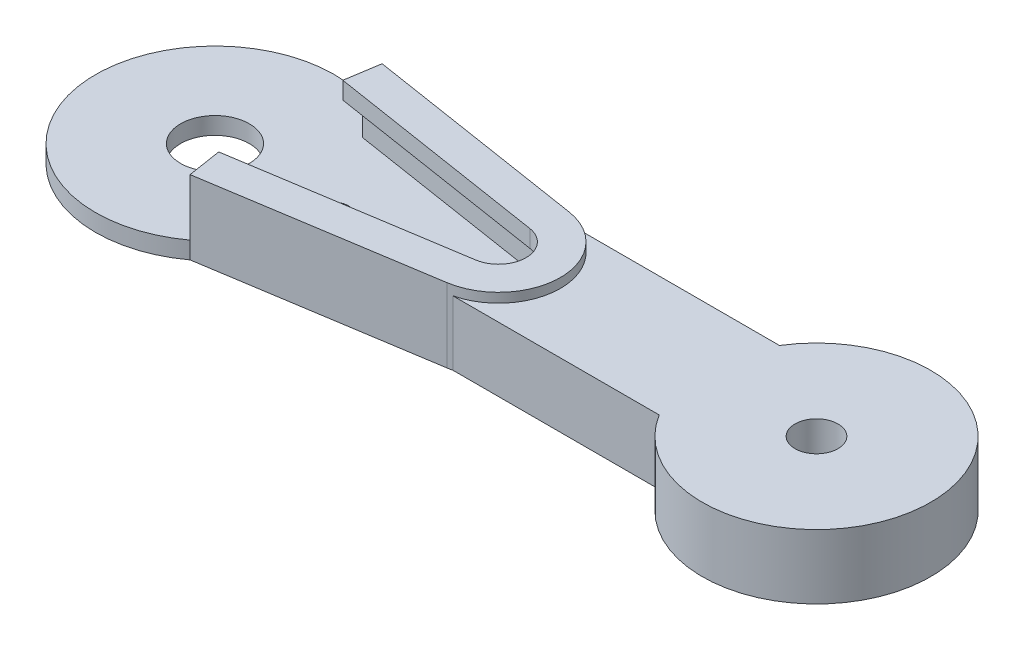
SolidWorks part; units mm, degrees
ref_plane "Front Plane" through (0, 0, 0) normal (0, 0, 1) x (1, 0, 0)
ref_plane "Top Plane" through (0, 0, 0) normal (0, 1, 0) x (1, 0, 0)
ref_plane "Right Plane" through (0, 0, 0) normal (1, 0, 0) x (0, 0, -1)
sketch "Sketch2" plane through (0, 0, 0) normal (0, 1, 0) x (1, 0, 0)
  circle A0 centre (0, 0) radius 6
  circle A1 centre (0, 0) radius 1.5
  dimension "D1" = 12
  dimension "D2" = 3
extrude "Boss-Extrude1" add sketch "Sketch2" along normal mid plane 2.3
sketch "Sketch3" plane through (0, 1.15, 0) normal (0, 1, 0) x (1, 0, 0)
  line L0 (0, 0) -> (0, 2.9) construction
  line L3 (0, 0) -> (0.376, 2.9763) construction
  line L52 (0.1074, 2.898) -> (0.3384, 2.6787)
  line L53 (-0.1074, 2.898) -> (-0.3384, 2.6787)
  line L54 (0.8248, 2.7802) -> (0.9939, 2.5104)
  line L55 (0.6167, 2.8337) -> (0.3384, 2.6787)
  line L56 (1.4903, 2.4878) -> (1.587, 2.1843)
  line L57 (1.302, 2.5913) -> (0.9939, 2.5104)
  line L58 (2.0621, 2.039) -> (2.0804, 1.721)
  line L59 (1.9055, 2.1861) -> (1.587, 2.1843)
  line L60 (2.5044, 1.4621) -> (2.443, 1.1496)
  line L61 (2.3893, 1.6435) -> (2.0804, 1.721)
  line L62 (2.7894, 0.7934) -> (2.6522, 0.5059)
  line L63 (2.723, 0.9977) -> (2.443, 1.1496)
  line L64 (2.899, 0.0748) -> (2.6947, -0.1695)
  line L65 (2.8855, 0.2892) -> (2.6522, 0.5059)
  line L66 (2.8265, -0.6486) -> (2.5679, -0.8343)
  line L67 (2.8668, -0.4375) -> (2.6947, -0.1695)
  line L68 (2.5765, -1.3311) -> (2.2797, -1.4467)
  line L69 (2.6679, -1.1367) -> (2.5679, -0.8343)
  line L70 (2.1645, -1.93) -> (1.8483, -1.9682)
  line L71 (2.3014, -1.7645) -> (2.2797, -1.4467)
  line L72 (1.6165, -2.4077) -> (1.3007, -2.366)
  line L73 (1.7903, -2.2814) -> (1.8483, -1.9682)
  line L74 (0.967, -2.734) -> (0.6715, -2.6152)
  line L75 (1.1667, -2.655) -> (1.3007, -2.366)
  line L76 (0.2566, -2.8886) -> (0, -2.7)
  line L77 (0.4698, -2.8617) -> (0.6715, -2.6152)
  line L78 (-0.4698, -2.8617) -> (-0.6715, -2.6152)
  line L79 (-0.2566, -2.8886) -> (0, -2.7)
  line L80 (-1.1667, -2.655) -> (-1.3007, -2.366)
  line L81 (-0.967, -2.734) -> (-0.6715, -2.6152)
  line L82 (-1.7903, -2.2814) -> (-1.8483, -1.9682)
  line L83 (-1.6165, -2.4077) -> (-1.3007, -2.366)
  line L84 (-2.3014, -1.7645) -> (-2.2797, -1.4467)
  line L85 (-2.1645, -1.93) -> (-1.8483, -1.9682)
  line L86 (-2.6679, -1.1367) -> (-2.5679, -0.8343)
  line L87 (-2.5765, -1.3311) -> (-2.2797, -1.4467)
  line L88 (-2.8668, -0.4375) -> (-2.6947, -0.1695)
  line L89 (-2.8265, -0.6486) -> (-2.5679, -0.8343)
  line L90 (-2.8855, 0.2892) -> (-2.6522, 0.5059)
  line L91 (-2.899, 0.0748) -> (-2.6947, -0.1695)
  line L92 (-2.723, 0.9977) -> (-2.443, 1.1496)
  line L93 (-2.7894, 0.7934) -> (-2.6522, 0.5059)
  line L94 (-2.3893, 1.6435) -> (-2.0804, 1.721)
  line L95 (-2.5044, 1.4621) -> (-2.443, 1.1496)
  line L96 (-1.9055, 2.1861) -> (-1.587, 2.1843)
  line L97 (-2.0621, 2.039) -> (-2.0804, 1.721)
  line L98 (-1.302, 2.5913) -> (-0.9939, 2.5104)
  line L99 (-1.4903, 2.4878) -> (-1.587, 2.1843)
  line L100 (-0.6167, 2.8337) -> (-0.3384, 2.6787)
  line L101 (-0.8248, 2.7802) -> (-0.9939, 2.5104)
  line L102 (-2.533, 1.6075) -> (-2.3893, 1.6435) construction
  line L103 (-2.533, 1.6075) -> (-2.5044, 1.4621) construction
  line L104 (-2.8532, 0.9271) -> (-2.723, 0.9977) construction
  line L105 (-2.8532, 0.9271) -> (-2.7894, 0.7934) construction
  line L106 (-2.9941, 0.1884) -> (-2.8855, 0.2892) construction
  line L107 (-2.9941, 0.1884) -> (-2.899, 0.0748) construction
  line L108 (-2.9469, -0.5621) -> (-2.8668, -0.4375) construction
  line L109 (-2.9469, -0.5621) -> (-2.8265, -0.6486) construction
  line L110 (0, 3) -> (0.1074, 2.898) construction
  line L111 (0, 2.9) -> (0, 3) construction
  line L112 (0, 3) -> (-0.1074, 2.898) construction
  line L113 (-0.7461, 2.9057) -> (-0.6167, 2.8337) construction
  line L114 (-0.7461, 2.9057) -> (-0.8248, 2.7802) construction
  line L115 (-1.4453, 2.6289) -> (-1.302, 2.5913) construction
  line L116 (-1.4453, 2.6289) -> (-1.4903, 2.4878) construction
  line L117 (-2.0536, 2.1869) -> (-1.9055, 2.1861) construction
  line L118 (-2.0536, 2.1869) -> (-2.0621, 2.039) construction
  line L119 (-2.7145, -1.2773) -> (-2.6679, -1.1367) construction
  line L120 (-2.7145, -1.2773) -> (-2.5765, -1.3311) construction
  line L121 (-2.3115, -1.9123) -> (-2.3014, -1.7645) construction
  line L122 (-2.3115, -1.9123) -> (-2.1645, -1.93) construction
  line L123 (-1.7634, -2.4271) -> (-1.7903, -2.2814) construction
  line L124 (-1.7634, -2.4271) -> (-1.6165, -2.4077) construction
  line L125 (-1.1044, -2.7893) -> (-1.1667, -2.655) construction
  line L126 (-1.1044, -2.7893) -> (-0.967, -2.734) construction
  line L127 (-0.376, -2.9763) -> (-0.4698, -2.8617) construction
  line L128 (-0.376, -2.9763) -> (-0.2566, -2.8886) construction
  line L129 (0.376, -2.9763) -> (0.2566, -2.8886) construction
  line L130 (0.376, -2.9763) -> (0.4698, -2.8617) construction
  line L131 (1.1044, -2.7893) -> (0.967, -2.734) construction
  line L132 (1.1044, -2.7893) -> (1.1667, -2.655) construction
  line L133 (1.7634, -2.4271) -> (1.6165, -2.4077) construction
  line L134 (1.7634, -2.4271) -> (1.7903, -2.2814) construction
  line L135 (2.3115, -1.9123) -> (2.3014, -1.7645) construction
  line L136 (2.3115, -1.9123) -> (2.1645, -1.93) construction
  line L137 (2.7145, -1.2773) -> (2.6679, -1.1367) construction
  line L138 (2.7145, -1.2773) -> (2.5765, -1.3311) construction
  line L139 (2.9469, -0.5621) -> (2.8668, -0.4375) construction
  line L140 (2.9469, -0.5621) -> (2.8265, -0.6486) construction
  line L141 (2.9941, 0.1884) -> (2.8855, 0.2892) construction
  line L142 (2.9941, 0.1884) -> (2.899, 0.0748) construction
  line L143 (2.8532, 0.9271) -> (2.723, 0.9977) construction
  line L144 (2.8532, 0.9271) -> (2.7894, 0.7934) construction
  line L145 (2.533, 1.6075) -> (2.3893, 1.6435) construction
  line L146 (2.533, 1.6075) -> (2.5044, 1.4621) construction
  line L147 (2.0536, 2.1869) -> (1.9055, 2.1861) construction
  line L148 (2.0536, 2.1869) -> (2.0621, 2.039) construction
  line L149 (1.4453, 2.6289) -> (1.302, 2.5913) construction
  line L150 (1.4453, 2.6289) -> (1.4903, 2.4878) construction
  line L151 (0.7461, 2.9057) -> (0.6167, 2.8337) construction
  line L152 (0.7461, 2.9057) -> (0.8248, 2.7802) construction
  circle A0 centre (0, 0) radius 4.4
  circle A1 centre (0, 0) radius 3 construction
  circle A2 centre (0, 0) radius 2.7 construction
  arc A3 (-0.6167, 2.8337) -> (-0.8248, 2.7802) centre (0, 0) ccw
  arc A4 (-0.1074, 2.898) -> (-0.6167, 2.8337) centre (0, 0) ccw construction
  arc A5 (-0.8248, 2.7802) -> (-1.302, 2.5913) centre (0, 0) ccw construction
  arc A6 (-1.302, 2.5913) -> (-1.4903, 2.4878) centre (0, 0) ccw
  arc A7 (-1.4903, 2.4878) -> (-1.9055, 2.1861) centre (0, 0) ccw construction
  arc A8 (-1.9055, 2.1861) -> (-2.0621, 2.039) centre (0, 0) ccw
  arc A9 (-2.0621, 2.039) -> (-2.3893, 1.6435) centre (0, 0) ccw construction
  arc A10 (-2.3893, 1.6435) -> (-2.5044, 1.4621) centre (0, 0) ccw
  arc A11 (-2.5044, 1.4621) -> (-2.723, 0.9977) centre (0, 0) ccw construction
  arc A12 (-2.723, 0.9977) -> (-2.7894, 0.7934) centre (0, 0) ccw
  arc A13 (-2.7894, 0.7934) -> (-2.8855, 0.2892) centre (0, 0) ccw construction
  arc A14 (-2.8855, 0.2892) -> (-2.899, 0.0748) centre (0, 0) ccw
  arc A15 (-2.899, 0.0748) -> (-2.8668, -0.4375) centre (0, 0) ccw construction
  arc A16 (-2.8668, -0.4375) -> (-2.8265, -0.6486) centre (0, 0) ccw
  arc A17 (-2.8265, -0.6486) -> (-2.6679, -1.1367) centre (0, 0) ccw construction
  arc A18 (-2.6679, -1.1367) -> (-2.5765, -1.3311) centre (0, 0) ccw
  arc A19 (-2.5765, -1.3311) -> (-2.3014, -1.7645) centre (0, 0) ccw construction
  arc A20 (-2.3014, -1.7645) -> (-2.1645, -1.93) centre (0, 0) ccw
  arc A21 (-2.1645, -1.93) -> (-1.7903, -2.2814) centre (0, 0) ccw construction
  arc A22 (-1.7903, -2.2814) -> (-1.6165, -2.4077) centre (0, 0) ccw
  arc A23 (-1.6165, -2.4077) -> (-1.1667, -2.655) centre (0, 0) ccw construction
  arc A24 (-1.1667, -2.655) -> (-0.967, -2.734) centre (0, 0) ccw
  arc A25 (-0.967, -2.734) -> (-0.4698, -2.8617) centre (0, 0) ccw construction
  arc A26 (-0.4698, -2.8617) -> (-0.2566, -2.8886) centre (0, 0) ccw
  arc A27 (-0.2566, -2.8886) -> (0.2566, -2.8886) centre (0, 0) ccw construction
  arc A28 (0.2566, -2.8886) -> (0.4698, -2.8617) centre (0, 0) ccw
  arc A29 (0.4698, -2.8617) -> (0.967, -2.734) centre (0, 0) ccw construction
  arc A30 (0.967, -2.734) -> (1.1667, -2.655) centre (0, 0) ccw
  arc A31 (1.1667, -2.655) -> (1.6165, -2.4077) centre (0, 0) ccw construction
  arc A32 (1.6165, -2.4077) -> (1.7903, -2.2814) centre (0, 0) ccw
  arc A33 (1.7903, -2.2814) -> (2.1645, -1.93) centre (0, 0) ccw construction
  arc A34 (2.1645, -1.93) -> (2.3014, -1.7645) centre (0, 0) ccw
  arc A35 (2.3014, -1.7645) -> (2.5765, -1.3311) centre (0, 0) ccw construction
  arc A36 (2.5765, -1.3311) -> (2.6679, -1.1367) centre (0, 0) ccw
  arc A37 (2.6679, -1.1367) -> (2.8265, -0.6486) centre (0, 0) ccw construction
  arc A38 (2.8265, -0.6486) -> (2.8668, -0.4375) centre (0, 0) ccw
  arc A39 (2.8668, -0.4375) -> (2.899, 0.0748) centre (0, 0) ccw construction
  arc A40 (2.899, 0.0748) -> (2.8855, 0.2892) centre (0, 0) ccw
  arc A41 (2.8855, 0.2892) -> (2.7894, 0.7934) centre (0, 0) ccw construction
  arc A42 (2.7894, 0.7934) -> (2.723, 0.9977) centre (0, 0) ccw
  arc A43 (2.723, 0.9977) -> (2.5044, 1.4621) centre (0, 0) ccw construction
  arc A44 (2.5044, 1.4621) -> (2.3893, 1.6435) centre (0, 0) ccw
  arc A45 (2.3893, 1.6435) -> (2.0621, 2.039) centre (0, 0) ccw construction
  arc A46 (2.0621, 2.039) -> (1.9055, 2.1861) centre (0, 0) ccw
  arc A47 (1.9055, 2.1861) -> (1.4903, 2.4878) centre (0, 0) ccw construction
  arc A48 (1.4903, 2.4878) -> (1.302, 2.5913) centre (0, 0) ccw
  arc A49 (1.302, 2.5913) -> (0.8248, 2.7802) centre (0, 0) ccw construction
  arc A50 (0.8248, 2.7802) -> (0.6167, 2.8337) centre (0, 0) ccw
  arc A51 (0.3635, 2.8771) -> (0.1074, 2.898) centre (0, 0) ccw construction
  arc A52 (0.1074, 2.898) -> (-0.1074, 2.898) centre (0, 0) ccw
  arc A53 (0.6167, 2.8337) -> (0.3635, 2.8771) centre (0, 0) ccw construction
  point P84 (0, 0)
  dimension "D1" = 8.8
  dimension "D2" = 5.4
  dimension "D3" = 6
  dimension "D6" = 5.8
  dimension "D4" = 7.2
  dimension "D5" = 25
extrude "Boss-Extrude2" add sketch "Sketch3" along normal blind 3.2
sketch "Sketch4" plane through (0, 0, 0) normal (0, 1, 0) x (1, 0, 0)
  line L0 (0, 0) -> (16, 0) construction
  line L1 (3.9686, 4.5) -> (16.8881, 2.4697)
  line L2 (3.9686, -4.5) -> (16.8881, -2.4697)
  line L3 (16, 0) -> (13, 0) construction
  circle A0 centre (0, 0) radius 6 construction
  arc A1 (3.9686, -4.5) -> (3.9686, 4.5) centre (0, 0) ccw
  arc A2 (16.8881, 2.4697) -> (16.8881, -2.4697) centre (16.5, 0) cw
  circle A3 centre (16, 0) radius 0.75
  circle A4 centre (13, 0) radius 0.75
  circle A5 centre (10, 0) radius 0.75
  circle A6 centre (7, 0) radius 0.75
  dimension "D3" = 2.5
  dimension "D5" = 1.5
  dimension "D2" = 9
  dimension "D7" = 3
  dimension "D4" = 0.5
  dimension "D1" = 16
  dimension "D6" = 4
extrude "Boss-Extrude3" add sketch "Sketch4" along normal mid plane 2.3
pattern_circular "CirPattern1" count 2 over 360 about axis through (0, 0, 0) along (0, 1, 0) of "Boss-Extrude3"
sketch "Sketch5" [suppressed] plane through (0, 0, 0) normal (0, 1, 0) x (1, 0, 0)
  line L0 (3, 7) -> (-3, 7) construction
  circle A0 centre (0, 0) radius 10
  circle A1 centre (0, 7) radius 0.75
  circle A2 centre (-3, 7) radius 0.75
  circle A3 centre (3, 7) radius 0.75
  circle A4 centre (7, 3) radius 0.75
  circle A5 centre (7, 0) radius 0.75
  circle A6 centre (7, -3) radius 0.75
  circle A7 centre (3, -7) radius 0.75
  circle A8 centre (0, -7) radius 0.75
  circle A9 centre (-3, -7) radius 0.75
  circle A10 centre (-7, -3) radius 0.75
  circle A11 centre (-7, 0) radius 0.75
  circle A12 centre (-7, 3) radius 0.75
  circle A13 centre (0, 0) radius 1.5 construction
  circle A14 centre (0, 0) radius 1.5
  point P8 (0, 7)
  point P31 (0, 0)
  dimension "D1" = 1.5
  dimension "D3" = 2.25
  dimension "D4" = 6
  dimension "D2" = 7
  dimension "D5" = 4
extrude "Boss-Extrude4" [suppressed] add sketch "Sketch5" along normal mid plane 2.3
sketch "Sketch6" plane through (0, -1.15, 0) normal (0, -1, 0) x (1, 0, 0)
  line L3 (16.9036, 2.5685) -> (3.9842, 4.5988)
  line L5 (16.9036, 2.5685) -> (3.9842, 4.5988)
  line L6 (17.0589, -3.5564) -> (4.1394, -5.5867)
  line L7 (16.9036, -2.5685) -> (3.9842, -4.5988)
  line L8 (16.9036, -2.5685) -> (3.9842, -4.5988)
  line L9 (17.0589, 3.5564) -> (4.1394, 5.5867)
  line L10 (4.1394, 5.5867) -> (3.9842, 4.5988)
  line L11 (3.9842, -4.5988) -> (4.1394, -5.5867)
  circle A3 centre (0, 0) radius 6.0846
  arc A4 (16.9036, -2.5685) -> (16.9036, 2.5685) centre (16.5, 0) ccw
  arc A5 (16.9036, -2.5685) -> (16.9036, 2.5685) centre (16.5, 0) ccw
  arc A6 (17.0589, -3.5564) -> (17.0589, 3.5564) centre (16.5, 0) ccw
  dimension "D1" = 0.1
  dimension "D2" = 0.1
  dimension "D3" = 1
extrude "Boss-Extrude5" add sketch "Sketch6" against normal blind 2.3 separate body contours L6 A6 L9 L10 L5 A5 L8 L11
sketch "Sketch7" plane through (0, -1.15, 0) normal (0, -1, 0) x (1, 0, 0)
  line L14 (4.1394, -5.5867) -> (17.0589, -3.5564)
  line L15 (17.0589, 3.5564) -> (4.1394, 5.5867)
  line L16 (4.1394, -5.5867) -> (17.0589, -3.5564)
  line L17 (17.0589, 3.5564) -> (4.1394, 5.5867)
  arc A2 (4.1394, 5.5867) -> (4.1394, -5.5867) centre (0, 0) ccw
  circle A5 centre (0, 0) radius 2
  arc A6 (17.0589, -3.5564) -> (17.0589, 3.5564) centre (16.5, 0) ccw
  arc A7 (17.0589, -3.5564) -> (17.0589, 3.5564) centre (16.5, 0) ccw
  dimension "D1" = 1
extrude "Boss-Extrude6" add sketch "Sketch7" along normal blind 1
sketch "Sketch10" plane through (0, -2.15, 0) normal (0, -1, 0) x (1, 0, 0)
  line L0 (0, 0) -> (20.1, 0) construction
  arc A0 (17.0589, -3.5564) -> (17.0589, 3.5564) centre (16.5, 0) ccw construction
  circle A3 centre (7, 0) radius 0.75
  circle A4 centre (10, 0) radius 0.75
  circle A5 centre (13, 0) radius 0.75
  circle A6 centre (16, 0) radius 0.75
  dimension "D1" = 1.5
  dimension "D2" = 7
  dimension "D3" = 4
extrude "Cut-Extrude2" cut sketch "Sketch10" against normal through all contours L0 A4 | L0 A5 | L0 A6 | A6 L0 | A5 L0 | A4 L0 | A3 L0 | L0 A3
sketch "Sketch12" plane through (0, 1.15, 0) normal (0, 1, 0) x (1, 0, 0)
  line L8 (-3.9686, 4.5) -> (-16.8881, 2.4697)
  line L9 (-16.8881, -2.4697) -> (-3.9686, -4.5)
  line L10 (3.9686, -4.5) -> (16.8881, -2.4697)
  line L12 (-3.9686, 4.5) -> (-16.8881, 2.4697)
  line L13 (-16.8881, -2.4697) -> (-3.9686, -4.5)
  line L16 (3.9686, -4.5) -> (16.8881, -2.4697)
  line L17 (16.8881, 2.4697) -> (3.9686, 4.5)
  line L18 (16.8881, 2.4697) -> (3.9686, 4.5)
  arc A8 (3.9686, 4.5) -> (-3.9686, 4.5) centre (0, 0) ccw
  arc A9 (-16.8881, 2.4697) -> (-16.8881, -2.4697) centre (-16.5, 0) ccw
  arc A10 (-3.9686, -4.5) -> (3.9686, -4.5) centre (0, 0) ccw
  arc A11 (16.8881, -2.4697) -> (16.8881, 2.4697) centre (16.5, 0) ccw
  arc A12 (3.9686, 4.5) -> (-3.9686, 4.5) centre (0, 0) ccw
  arc A13 (-16.8881, 2.4697) -> (-16.8881, -2.4697) centre (-16.5, 0) ccw
  arc A14 (-3.9686, -4.5) -> (3.9686, -4.5) centre (0, 0) ccw
  arc A17 (16.8881, -2.4697) -> (16.8881, 2.4697) centre (16.5, 0) ccw
  dimension "D1" = 0
extrude "Cut-Extrude4" cut sketch "Sketch12" against normal blind 2.3
sketch "Sketch13" plane through (0, 4.35, 0) normal (0, 1, 0) x (1, 0, 0)
  circle A3 centre (0, 0) radius 4.4
  circle A4 centre (0, 0) radius 4.4
  dimension "D1" = 0
extrude "Cut-Extrude5" cut sketch "Sketch13" against normal blind 3.3
sketch "Sketch9" plane through (0, 1.15, 0) normal (0, 1, 0) x (1, 0, 0)
  line L0 (3.8289, -3.6109) -> (16.7484, -1.5806)
  line L1 (16.7484, 1.5806) -> (3.8289, 3.6109)
  line L2 (3.8289, 3.6109) -> (3.9842, 4.5988)
  line L3 (3.8289, -3.6109) -> (3.9842, -4.5988)
  line L5 (4.1394, 5.5867) -> (3.9842, 4.5988)
  line L7 (4.1394, -5.5867) -> (17.0589, -3.5564)
  line L8 (17.0589, 3.5564) -> (4.1394, 5.5867)
  line L9 (4.1394, -5.5867) -> (17.0589, -3.5564)
  line L10 (17.0589, 3.5564) -> (4.1394, 5.5867)
  line L11 (3.9842, -4.5988) -> (4.1394, -5.5867)
  line L30 (3.9842, -4.5988) -> (16.9036, -2.5685)
  line L31 (16.9036, 2.5685) -> (3.9842, 4.5988)
  line L32 (3.9842, -4.5988) -> (16.9036, -2.5685)
  line L33 (16.9036, 2.5685) -> (3.9842, 4.5988)
  arc A0 (16.7484, -1.5806) -> (16.7484, 1.5806) centre (16.5, 0) ccw
  arc A2 (17.0589, -3.5564) -> (17.0589, 3.5564) centre (16.5, 0) ccw
  arc A3 (17.0589, -3.5564) -> (17.0589, 3.5564) centre (16.5, 0) ccw
  arc A9 (16.9036, -2.5685) -> (16.9036, 2.5685) centre (16.5, 0) ccw
  arc A10 (16.9036, -2.5685) -> (16.9036, 2.5685) centre (16.5, 0) ccw
  line M4 (17.0589, 3.5564) -> (4.1394, 5.5867)
  line M5 (4.1394, 5.5867) -> (3.9842, 4.5988)
  line M6 (3.9842, 4.5988) -> (16.9036, 2.5685)
  arc M7 (16.9036, 2.5685) -> (16.9036, -2.5685) centre (16.5, 0) cw
  line M8 (16.9036, -2.5685) -> (3.9842, -4.5988)
  line M9 (3.9842, -4.5988) -> (4.1394, -5.5867)
  line M10 (4.1394, -5.5867) -> (17.0589, -3.5564)
  arc M11 (17.0589, -3.5564) -> (17.0589, 3.5564) centre (16.5, 0) ccw
  dimension "D1" = 1
  dimension "D2" = 0
  dimension "D3" = 1
extrude "Boss-Extrude8" add sketch "Sketch9" along normal blind 1 contours M11 M4 M5 M6 M7 M8 M9 M10 | A0 L0 L3 L2 L1 M8 M7 M6
sketch "Sketch14" plane through (0, -2.15, 0) normal (0, -1, 0) x (1, 0, 0)
  line L0 (0, 0) -> (35, 0) construction
  line L1 (17.0589, 3.5564) -> (17.0589, -3.5564) construction
  line L3 (17.0589, 0) -> (30.837, 0)
  line L4 (17.0589, 0) -> (17.0589, 3.5)
  line L5 (17.0589, 3.5) -> (30.837, 3.5)
  line L6 (30.837, 0) -> (30.837, 3.5)
  line L7 (17.0589, 0) -> (30.837, 0)
  line L8 (17.0589, 0) -> (17.0589, -3.5)
  line L9 (17.0589, -3.5) -> (30.837, -3.5)
  line L10 (30.837, 0) -> (30.837, -3.5)
  circle A0 centre (35, 0) radius 7
  circle A1 centre (35, 0) radius 1.25
  arc M7 (17.0589, -3.5564) -> (17.0589, 3.5564) centre (16.5, 0) ccw
  dimension "D2" = 2.5
  dimension "D1" = 35
  dimension "D3" = 3.5
  dimension "D4" = 3.5
extrude "Boss-Extrude9" add sketch "Sketch14" against normal blind 3.9 contours A0 L3 L9 M7 | A0 L5 L3 M7 | L9 A0 L5 L6 L10 A1 | L7 A0 L9 L10 | L5 A0 L7 L6
sketch "Sketch15" plane through (0, -2.15, 0) normal (0, -1, 0) x (1, 0, 0)
  line L1 (28.9378, 3.5) -> (35, 3.5)
  line L2 (28.9378, 3.5) -> (28.9378, -3.5)
  line L3 (28.9378, -3.5) -> (35, -3.5)
  line L4 (35, 3.5) -> (35, -3.5)
  circle A0 centre (35, 0) radius 6.65
  circle A1 centre (35, 0) radius 7
  arc M9 (28.9378, -3.5) -> (28.9378, 3.5) centre (35, 0) ccw
  dimension "D1" = 13.3
extrude "Cut-Extrude6" cut sketch "Sketch15" against normal blind 10 contours A0 L3 L1 M9
sketch "Sketch17" plane through (0, 1.75, 0) normal (0, 1, 0) x (1, 0, 0)
  line L4 (17.3426, -3.5) -> (29.3456, -3.5)
  line L5 (29.3456, 3.5) -> (17.3426, 3.5)
  line L6 (17.3426, -3.5) -> (29.3456, -3.5)
  line L7 (29.3456, 3.5) -> (17.3426, 3.5)
  arc A4 (29.3456, -3.5) -> (29.3456, 3.5) centre (35, 0) ccw
  arc A5 (17.3426, -3.5) -> (17.3426, 3.5) centre (16.5, 0) ccw
  arc A6 (29.3456, -3.5) -> (29.3456, 3.5) centre (35, 0) ccw
  arc A7 (17.3426, -3.5) -> (17.3426, 3.5) centre (16.5, 0) ccw
  dimension "D1" = 0
extrude "Cut-Extrude8" cut sketch "Sketch17" against normal blind 0.15 and the other way through all
equation "\"N_hole\"= 4"
equation "\"N_horn\"= 2"
equation "\"D6@Sketch4\"=\"N_hole\""
equation "\"D1@CirPattern1\"=\"N_horn\""
equation "\"D1@Sketch4\"=(\"N_hole\" - 1) *3 +7"
